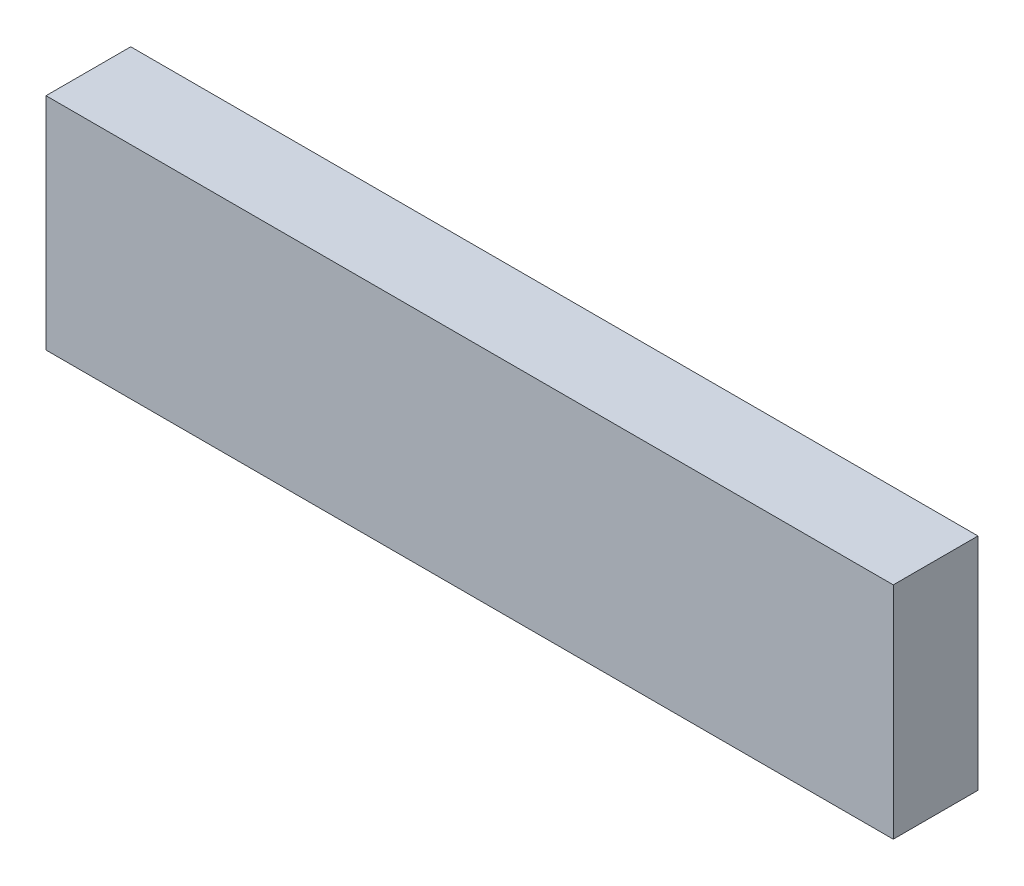
SolidWorks part; units mm, degrees
ref_plane "前基準面" through (0, 0, 0) normal (0, 0, 1) x (1, 0, 0)
ref_plane "上基準面" through (0, 0, 0) normal (0, 1, 0) x (1, 0, 0)
ref_plane "右基準面" through (0, 0, 0) normal (1, 0, 0) x (0, 0, -1)
sketch "草圖1" plane through (0, 0, 0) normal (0, 0, 1) x (1, 0, 0)
  line L1 (-24.0943, 8.2137) -> (25.9057, 8.2137)
  line L2 (-24.0943, 8.2137) -> (-24.0943, -4.7863)
  line L3 (-24.0943, -4.7863) -> (25.9057, -4.7863)
  line L4 (25.9057, 8.2137) -> (25.9057, -4.7863)
  dimension "D1" = 50
  dimension "D2" = 13
extrude "填料-伸長1" add sketch "草圖1" along normal blind 5
